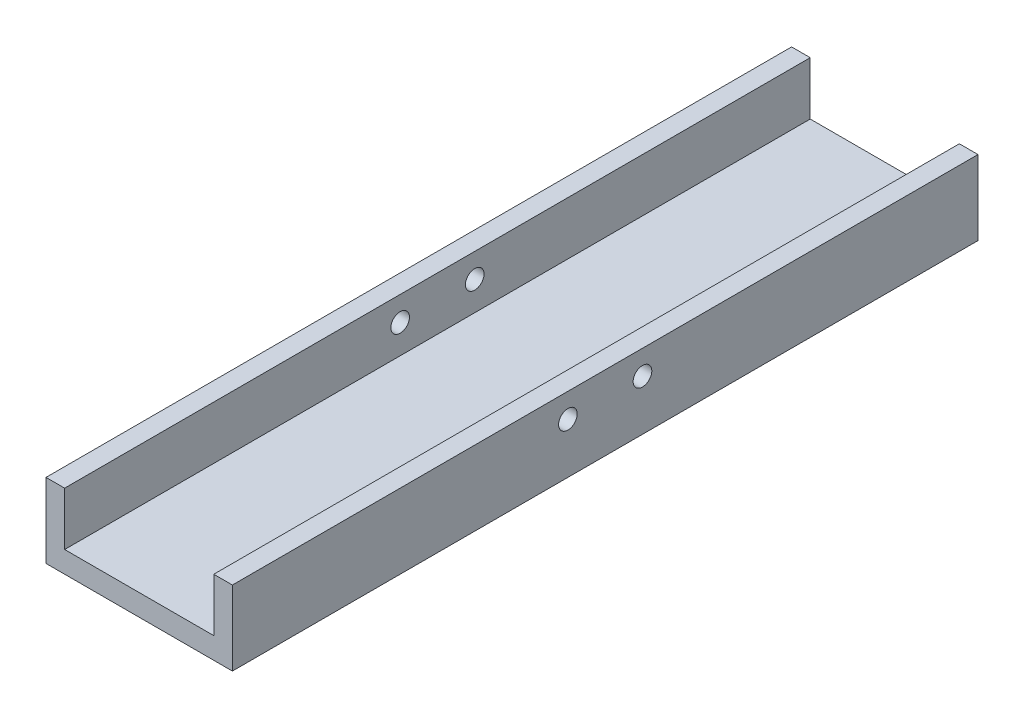
SolidWorks part; units mm, degrees
ref_plane "Ebene vorne" through (0, 0, 0) normal (0, 0, 1) x (1, 0, 0)
ref_plane "Ebene oben" through (0, 0, 0) normal (0, 1, 0) x (1, 0, 0)
ref_plane "Ebene rechts" through (0, 0, 0) normal (1, 0, 0) x (0, 0, -1)
sketch "Skizze1" plane through (0, 0, 0) normal (0, 0, 1) x (1, 0, 0)
  line L1 (-4.6579, -15.7449) -> (45.3421, -15.7449)
  line L2 (-4.6579, -15.7449) -> (-4.6579, 4.2551)
  line L3 (-4.6579, 4.2551) -> (45.3421, 4.2551)
  line L4 (45.3421, -15.7449) -> (45.3421, 4.2551)
  dimension "D1" = 50
  dimension "D2" = 20
extrude "Aufsatz-Linear austragen1" add sketch "Skizze1" along normal blind 200
sketch "Skizze2" plane through (0, 0, 0) normal (1, 0, 0) x (0, 0, -1)
  line L0 (0, -15.7449) -> (0, 4.2551) construction
  line L1 (-115, -3.2449) -> (-85, -3.2449)
  line L2 (-115, -3.2449) -> (-115, -8.2449)
  line L3 (-115, -8.2449) -> (-85, -8.2449)
  line L4 (-85, -3.2449) -> (-85, -8.2449)
  line L5 (0, -5.7449) -> (-118.0474, -5.7449) construction
  line L6 (-100, 4.2551) -> (-100, -15.7449) construction
  line L7 (-200, 4.2551) -> (0, 4.2551) construction
  line L8 (-200, -15.7449) -> (0, -15.7449) construction
  point P4 (0, -5.7449)
  point P6 (-85, -5.7449)
  point P16 (0, 0)
  point P20 (-100, -3.2449)
  dimension "D1" = 30
  dimension "D2" = 5
sketch "Skizze3" plane through (0, 0, 0) normal (1, 0, 0) x (0, 0, -1)
  line L0 (-200, 4.2551) -> (0, 4.2551) construction
  line L2 (-100, 4.2551) -> (-100, -15.7449) construction
  circle A0 centre (-90, -2.2449) radius 2.5
  circle A1 centre (-110, -2.2449) radius 2.5
  point P8 (0, 0)
  point P10 (-100, 4.2551)
  dimension "D1" = 6.5
  dimension "D3" = 5
  dimension "D2" = 20
extrude "Schnitt-Linear austragen1" cut sketch "Skizze3" against normal through all both and the other way through all
sketch "Skizze4" plane through (0, 0, 0) normal (0, 1, 0) x (1, 0, 0)
  line L0 (45.3421, -200) -> (-4.6579, -200) construction
  line L1 (45.3421, 0) -> (-4.6579, 0) construction
  line L2 (-4.6579, -200) -> (-4.6579, 0) construction
  line L3 (40.3421, -200) -> (0.3421, -200)
  line L4 (40.3421, -200) -> (40.3421, 0)
  line L5 (40.3421, 0) -> (0.3421, 0)
  line L6 (0.3421, -200) -> (0.3421, 0)
  line L7 (20.3421, -200) -> (20.3421, 0) construction
  point P0 (40.3421, -200)
  point P1 (2.0643, -200)
  point P4 (38.5236, 0)
  point P5 (0.3421, 0)
  point P16 (0, 0)
  dimension "D1" = 5
extrude "Schnitt-Linear austragen2" cut sketch "Skizze4" against normal blind 20 from offset 10
